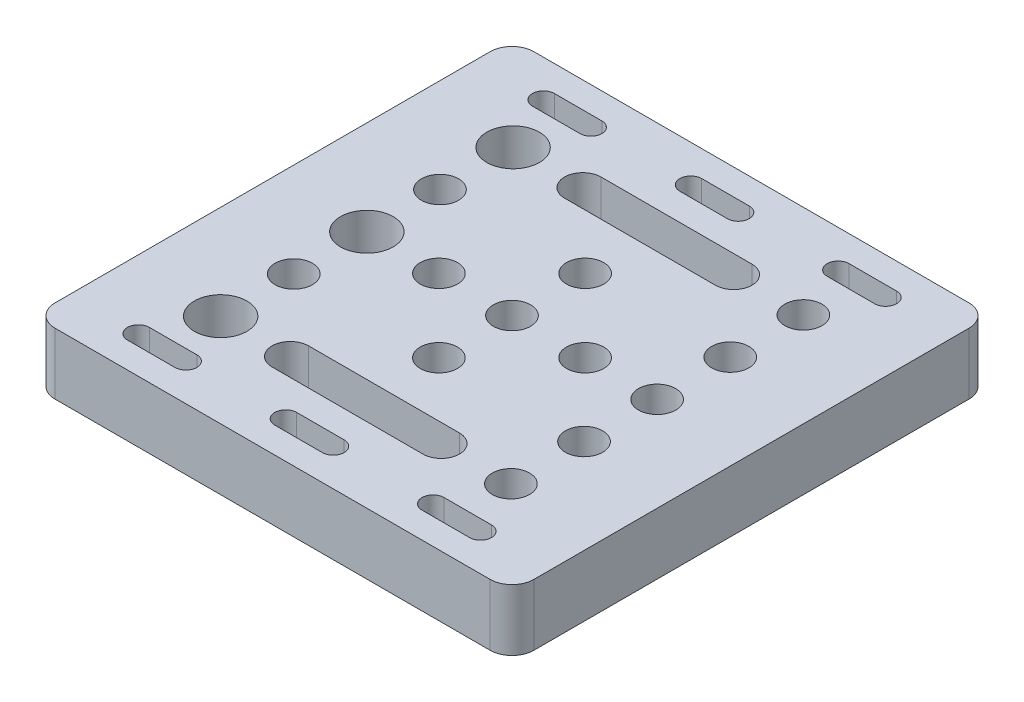
SolidWorks part; units mm, degrees
material "6061-T6 (SS)"
ref_plane "Front Plane" through (0, 0, 0) normal (0, 0, 1) x (1, 0, 0)
ref_plane "Top Plane" through (0, 0, 0) normal (0, 1, 0) x (1, 0, 0)
ref_plane "Right Plane" through (0, 0, 0) normal (1, 0, 0) x (0, 0, -1)
sketch "Sketch1" plane through (0, 0, 0) normal (0, 1, 0) x (1, 0, 0)
  line L0 (0, 0) -> (32.75, 0) construction
  line L1 (29.75, -32.75) -> (-29.75, -32.75)
  line L2 (32.75, -29.75) -> (32.75, 29.75)
  line L3 (29.75, 32.75) -> (-29.75, 32.75)
  line L4 (-32.75, -29.75) -> (-32.75, 29.75)
  line L5 (0, 32.75) -> (0, 0) construction
  line L9 (10.32, 20) -> (-10.32, 20) construction
  line L10 (10.32, 17.5) -> (-10.32, 17.5)
  line L11 (10.32, 22.5) -> (-10.32, 22.5)
  line L12 (3.25, 27.7) -> (-3.25, 27.7) construction
  line L13 (3.25, 26.2) -> (-3.25, 26.2)
  line L14 (3.25, 29.2) -> (-3.25, 29.2)
  line L15 (-16.9, 27.7) -> (-23.4, 27.7) construction
  line L16 (-16.9, 26.2) -> (-23.4, 26.2)
  line L17 (-16.9, 29.2) -> (-23.4, 29.2)
  line L18 (16.9, 27.7) -> (23.4, 27.7) construction
  line L19 (16.9, 26.2) -> (23.4, 26.2)
  line L20 (16.9, 29.2) -> (23.4, 29.2)
  line L21 (10.32, -20) -> (-10.32, -20) construction
  line L22 (10.32, -17.5) -> (-10.32, -17.5)
  line L23 (10.32, -22.5) -> (-10.32, -22.5)
  line L24 (-16.9, -27.7) -> (-23.4, -27.7) construction
  line L25 (-16.9, -26.2) -> (-23.4, -26.2)
  line L26 (-16.9, -29.2) -> (-23.4, -29.2)
  line L27 (3.25, -27.7) -> (-3.25, -27.7) construction
  line L28 (3.25, -26.2) -> (-3.25, -26.2)
  line L29 (3.25, -29.2) -> (-3.25, -29.2)
  line L30 (16.9, -27.7) -> (23.4, -27.7) construction
  line L31 (16.9, -26.2) -> (23.4, -26.2)
  line L32 (16.9, -29.2) -> (23.4, -29.2)
  arc A0 (-29.75, -32.75) -> (-32.75, -29.75) centre (-29.75, -29.75) cw
  arc A1 (29.75, -32.75) -> (32.75, -29.75) centre (29.75, -29.75) ccw
  arc A2 (32.75, 29.75) -> (29.75, 32.75) centre (29.75, 29.75) ccw
  arc A3 (-29.75, 32.75) -> (-32.75, 29.75) centre (-29.75, 29.75) ccw
  circle A5 centre (0, 10) radius 2.55
  circle A6 centre (0, 0) radius 2.55
  circle A7 centre (10, 0) radius 2.55
  circle A8 centre (-10, 0) radius 2.55
  circle A9 centre (-19.85, 20) radius 3.6
  circle A10 centre (-19.85, 0) radius 3.6
  circle A11 centre (-19.85, -20) radius 3.6
  circle A16 centre (-19.85, 10) radius 2.55
  circle A24 centre (19.85, 20) radius 2.55
  circle A25 centre (19.85, 0) radius 2.55
  circle A27 centre (19.85, -20) radius 2.55
  circle A30 centre (0, -10) radius 2.55
  circle A46 centre (19.85, 10) radius 2.55
  circle A54 centre (19.85, -10) radius 2.55
  circle A63 centre (-19.85, -10) radius 2.55
  arc A67 (10.32, 17.5) -> (10.32, 22.5) centre (10.32, 20) ccw
  arc A68 (-10.32, 22.5) -> (-10.32, 17.5) centre (-10.32, 20) ccw
  arc A69 (3.25, 26.2) -> (3.25, 29.2) centre (3.25, 27.7) ccw
  arc A70 (-3.25, 29.2) -> (-3.25, 26.2) centre (-3.25, 27.7) ccw
  arc A71 (-16.9, 26.2) -> (-16.9, 29.2) centre (-16.9, 27.7) ccw
  arc A72 (-23.4, 29.2) -> (-23.4, 26.2) centre (-23.4, 27.7) ccw
  arc A73 (16.9, 26.2) -> (16.9, 29.2) centre (16.9, 27.7) cw
  arc A74 (23.4, 29.2) -> (23.4, 26.2) centre (23.4, 27.7) cw
  arc A75 (10.32, -17.5) -> (10.32, -22.5) centre (10.32, -20) cw
  arc A76 (-10.32, -22.5) -> (-10.32, -17.5) centre (-10.32, -20) cw
  arc A77 (-16.9, -26.2) -> (-16.9, -29.2) centre (-16.9, -27.7) cw
  arc A78 (-23.4, -29.2) -> (-23.4, -26.2) centre (-23.4, -27.7) cw
  arc A79 (3.25, -26.2) -> (3.25, -29.2) centre (3.25, -27.7) cw
  arc A80 (-3.25, -29.2) -> (-3.25, -26.2) centre (-3.25, -27.7) cw
  arc A81 (16.9, -26.2) -> (16.9, -29.2) centre (16.9, -27.7) ccw
  arc A82 (23.4, -29.2) -> (23.4, -26.2) centre (23.4, -27.7) ccw
  point P0 (0, 0)
  point P149 (0, 20)
  point P156 (0, 27.7)
  point P162 (-20.15, 27.7)
  point P170 (20.15, 27.7)
  point P177 (0, -20)
  point P184 (-20.15, -27.7)
  point P191 (0, -27.7)
  point P198 (20.15, -27.7)
  dimension "D2" = 3
  dimension "D3" = 5.1
  dimension "D5" = 7.2
  dimension "D10" = 10
  dimension "D1" = 65.5
  dimension "D4" = 10
  dimension "D6" = 40
  dimension "D8" = 12.9
  dimension "D9" = 65.5
  dimension "D14" = 10
  dimension "D16" = 39.7
  dimension "D25" = 5
  dimension "D26" = 20.64
  dimension "D27" = 6.5
  dimension "D28" = 3
  dimension "D29" = 20.15
  dimension "D30" = 40
  dimension "D31" = 55.4
extrude "Boss-Extrude1" add sketch "Sketch1" along normal blind 8.4
